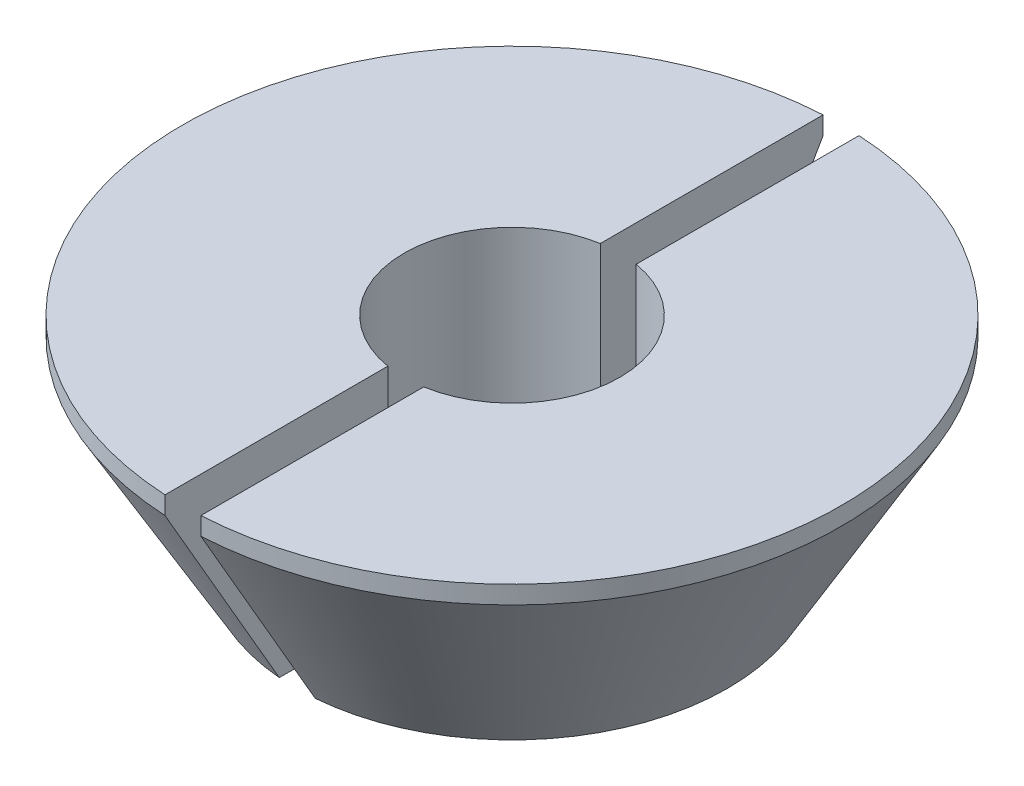
SolidWorks part; units mm, degrees
ref_plane "Front Plane" through (0, 0, 0) normal (0, 0, 1) x (1, 0, 0)
ref_plane "Top Plane" through (0, 0, 0) normal (0, 1, 0) x (1, 0, 0)
ref_plane "Right Plane" through (0, 0, 0) normal (1, 0, 0) x (0, 0, -1)
sketch "Sketch1" plane through (0, 0, 0) normal (0, 0, 1) x (1, 0, 0)
  line L0 (0, 0) -> (0, 3.6753) construction
  line L1 (1.5, 0) -> (3, 0)
  line L2 (3, 0) -> (4.5877, 2.75)
  line L3 (4.5877, 2.75) -> (4.5877, 3)
  line L4 (4.5877, 3) -> (1.5, 3)
  line L5 (1.5, 3) -> (1.5, 0)
  point P5 (0, 0)
  dimension "D1" = 1.5
  dimension "D2" = 1.5
  dimension "D3" = 3
  dimension "D4" = 0.25
  dimension "D5" = 60
revolve "Revolve1" add sketch "Sketch1" angle 360 about L0
sketch "Sketch2" plane through (0, 3, 0) normal (0, 1, 0) x (1, 0, 0)
  line L1 (0.25, -5) -> (-0.25, -5)
  line L2 (0.25, -5) -> (0.25, 5)
  line L3 (0.25, 5) -> (-0.25, 5)
  line L4 (-0.25, -5) -> (-0.25, 5)
  line L5 (0.25, -5) -> (-0.25, 5) construction
  line L6 (0.25, 5) -> (-0.25, -5) construction
  point P0 (0, 0)
  dimension "D1" = 10
  dimension "D2" = 0.5
extrude "Cut-Extrude1" cut sketch "Sketch2" against normal through all
